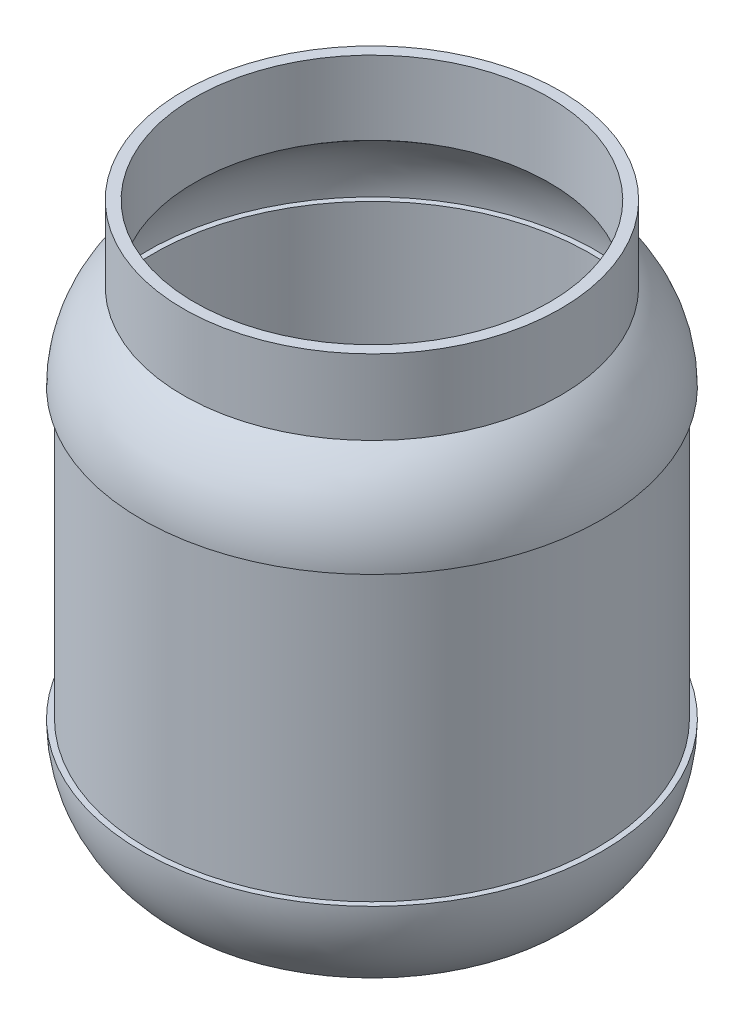
SolidWorks part; units mm, degrees
ref_plane "Front Plane" through (0, 0, 0) normal (0, 0, 1) x (1, 0, 0)
ref_plane "Top Plane" through (0, 0, 0) normal (0, 1, 0) x (1, 0, 0)
ref_plane "Right Plane" through (0, 0, 0) normal (1, 0, 0) x (0, 0, -1)
sketch "Sketch1" plane through (0, 0, 0) normal (0, 0, 1) x (1, 0, 0)
  line L0 (0, 0) -> (0, 146.05)
  line L1 (0, 0) -> (12.7, 0)
  line L2 (12.7, 0) -> (14.732, -2.1167)
  line L3 (14.732, -2.1167) -> (25.146, -2.1167)
  line L4 (25.146, -2.1167) -> (27.178, -4.2333)
  line L5 (27.178, -4.2333) -> (48.768, -4.2333)
  line L6 (48.768, -4.2333) -> (50.8, -6.35)
  line L7 (50.8, -6.35) -> (53.975, -6.35)
  line L8 (63.5, 19.05) -> (63.5, 100.33)
  line L9 (53.34, 124.841) -> (53.34, 146.05)
  line L10 (53.34, 146.05) -> (0, 146.05)
  line L11 (63.5, 100.33) -> (65.0875, 100.33)
  line L12 (63.5, 19.05) -> (65.0875, 19.05)
  line L13 (65.0875, 100.33) -> (65.0875, 19.05) construction
  line L14 (12.7, 0) -> (12.7, -2.1167) construction
  line L15 (12.7, -2.1167) -> (14.732, -2.1167) construction
  line L16 (14.732, -4.2333) -> (27.178, -4.2333) construction
  line L17 (27.178, -6.35) -> (50.8, -6.35) construction
  line L18 (27.178, -6.35) -> (27.178, -4.2333) construction
  line L19 (14.732, -4.2333) -> (14.732, -2.1167) construction
  line L23 (1.5875, 1.5875) -> (13.3766, 1.5875)
  line L24 (13.3766, 1.5875) -> (15.4086, -0.5292)
  line L25 (15.4086, -0.5292) -> (25.8226, -0.5292)
  line L26 (25.8226, -0.5292) -> (27.8546, -2.6458)
  line L27 (27.8546, -2.6458) -> (49.4446, -2.6458)
  line L28 (49.4446, -2.6458) -> (51.4766, -4.7625)
  line L29 (51.4766, -4.7625) -> (53.3454, -4.7625)
  line L30 (61.9125, 17.4625) -> (63.4618, 17.4625)
  line L31 (61.9125, 17.4625) -> (61.9125, 101.9175)
  line L32 (61.9125, 101.9175) -> (63.4578, 101.9175)
  line L33 (1.5875, 1.5875) -> (1.5875, 144.4625) construction
  line L34 (1.5875, 1.5875) -> (0, 1.5875)
  line L35 (50.165, 146.05) -> (50.165, 125.199)
  line L36 (51.7525, 124.068) -> (51.7525, 144.4625) construction
  line L37 (51.7525, 144.4625) -> (1.5875, 144.4625) construction
  arc A0 (65.0875, 100.33) -> (53.34, 124.841) centre (33.6428, 100.33) ccw
  arc A1 (65.0875, 19.05) -> (53.975, -6.35) centre (30.5027, 19.05) cw
  arc A2 (63.4618, 17.4625) -> (53.3454, -4.7625) centre (30.5027, 19.05) cw
  arc A3 (63.4578, 101.9175) -> (51.7525, 124.068) centre (33.6428, 100.33) ccw
  arc A4 (51.7525, 124.068) -> (50.165, 125.199) centre (33.6428, 100.33) ccw
  dimension "D1" = 63.5
  dimension "D2" = 1.5875
  dimension "D3" = 81.28
  dimension "D4" = 152.4
  dimension "D5" = 53.34
  dimension "D6" = 21.209
  dimension "D7" = 6.35
  dimension "D8" = 53.975
  dimension "D9" = 25.4
  dimension "D10" = 12.7
  dimension "D11" = 10.414
  dimension "D12" = 21.59
  dimension "D13" = 50.8
  dimension "D15" = 3.175
  dimension "D14" = 1.5875
revolve "Revolve1" add sketch "Sketch1" angle 360 about L0
